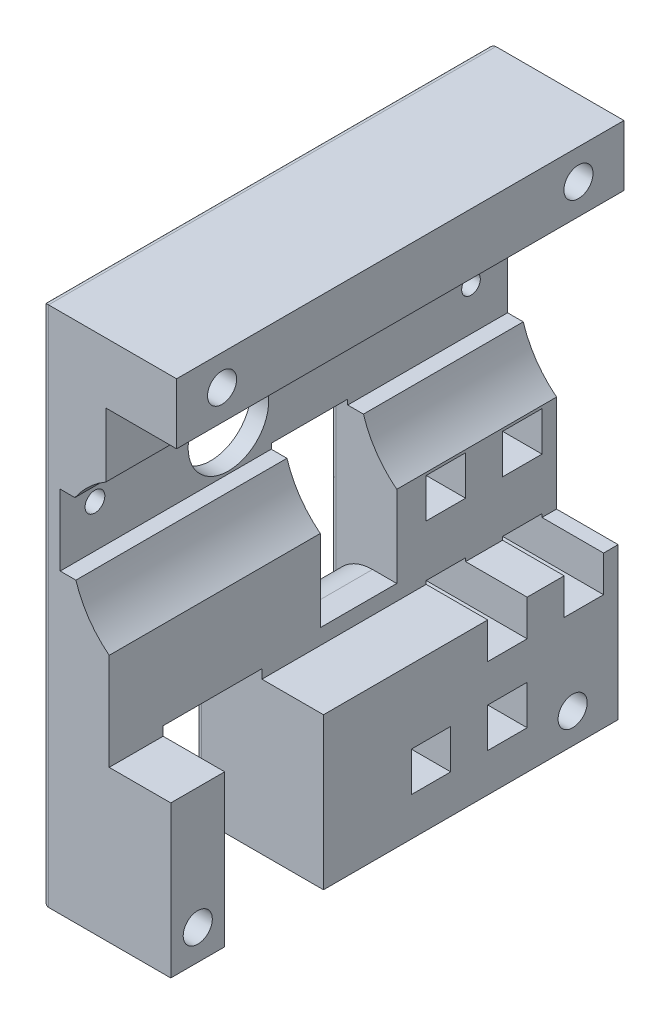
SolidWorks part; units mm, degrees
ref_plane "Front" through (0, 0, 0) normal (0, 0, 1) x (1, 0, 0)
ref_plane "Top" through (0, 0, 0) normal (0, 1, 0) x (1, 0, 0)
ref_plane "Right" through (0, 0, 0) normal (1, 0, 0) x (0, 0, -1)
sketch "Profile" plane through (0, 0, 0) normal (0, 0, 1) x (1, 0, 0)
  line L0 (9.3013, -54.1947) -> (9.3013, -29.1947)
  line L1 (-11.8487, -54.1947) -> (9.3013, -54.1947)
  line L2 (-11.8487, -54.1947) -> (-11.8487, 31.8453)
  line L3 (-11.8487, 31.8453) -> (10.2613, 31.8453)
  line L4 (10.2613, 21.8453) -> (10.2613, 31.8453)
  line L7 (9.3013, -29.1947) -> (-0.8487, -29.1947)
  line L8 (-0.8487, -29.1947) -> (-0.8487, -13.1966)
  line L10 (10.2613, 21.8453) -> (-1.3887, 21.8453)
  line L11 (-1.3887, 21.8453) -> (-1.3887, 11.2835)
  line L12 (-6.5097, 6.4953) -> (-8.9287, 6.4953)
  line L13 (-8.9287, 6.4953) -> (-8.9287, -5.2047)
  line L14 (-8.9287, -5.2047) -> (-6.3407, -5.2047)
  arc A0 (-6.3407, -5.2047) -> (-0.8487, -13.1966) centre (9.1973, -0.41) ccw
  arc A1 (-6.5097, 6.4953) -> (-1.3887, 11.2835) centre (6.8957, -2.7089) cw
  point P0 (0, 0)
  dimension "D15" = 16.261
  dimension "D16" = 16.261
  dimension "D1" = 86.04
  dimension "D2" = 22.11
  dimension "D3" = 10
  dimension "D4" = 25
  dimension "D5" = 21.15
  dimension "D6" = 10.15
  dimension "D7" = 11.65
  dimension "D8" = 10.5617
  dimension "D9" = 15.9981
  dimension "D10" = 2.588
  dimension "D11" = 11.7
  dimension "D12" = 2.4191
  dimension "D13" = 5.492
  dimension "D14" = 23.99
extrude "ProfileExtrude" add sketch "Profile" along normal blind 73.76
sketch "HoseWindow" plane through (-11.8487, 0, 0) normal (-1, 0, 0) x (0, 0, 1)
  line L0 (73.76, -54.1947) -> (0, -54.1947) construction
  line L1 (64.87, -54.1947) -> (48.58, -54.1947)
  line L2 (64.87, -54.1947) -> (64.87, -27.6947)
  line L3 (64.87, -27.6947) -> (48.58, -27.6947)
  line L4 (48.58, -54.1947) -> (48.58, -27.6947)
  dimension "D1" = 16.29
  dimension "D2" = 26.5
  dimension "D3" = 8.89
extrude "HoseWindowCut" cut sketch "HoseWindow" against normal through all
sketch "CageScrews" plane through (-11.8487, 0, 0) normal (-1, 0, 0) x (0, 0, 1)
  line L0 (73.76, 31.8453) -> (0, 31.8453) construction
  line L1 (0, 31.8453) -> (0, -54.1947) construction
  line L2 (73.76, 31.8453) -> (73.76, -54.1947) construction
  line L3 (73.76, -54.1947) -> (64.87, -54.1947) construction
  line L4 (48.58, -54.1947) -> (0, -54.1947) construction
  circle A0 centre (7.5, 26.8453) radius 2.4
  circle A1 centre (66.26, 26.8453) radius 2.4
  circle A2 centre (7.5, -49.1947) radius 2.4
  circle A3 centre (69.31, -49.1947) radius 2.4
  dimension "D1" = 4.8
  dimension "D2" = 5
  dimension "D3" = 7.5
  dimension "D4" = 7.5
  dimension "D5" = 5
  dimension "D6" = 5
  dimension "D7" = 4.45
  dimension "D8" = 5
  dimension "D9" = 7.5
extrude "CageScrewsCut" cut sketch "CageScrews" against normal through all
sketch "AxleHole" plane through (-11.8487, 0, 0) normal (-1, 0, 0) x (0, 0, 1)
  line L0 (46.03, -4.7837) -> (46.03, 6.7405) construction
  line L1 (47.361, 8.3595) -> (47.361, 6.7405)
  line L2 (47.361, 6.7405) -> (44.699, 6.7405)
  line L3 (44.699, 6.7405) -> (44.699, 8.3595)
  line L5 (48.58, -54.1947) -> (0, -54.1947) construction
  line L6 (0, 31.8453) -> (0, -54.1947) construction
  line L7 (39.391, 1.8553) -> (52.669, 1.8553) construction
  arc A0 (44.699, 8.3595) -> (47.361, 8.3595) centre (46.03, 1.8553) ccw
  dimension "D1" = 13.278
  dimension "D2" = 1.331
  dimension "D3" = 1.619
  dimension "D4" = 1.619
  dimension "D5" = 46.03
  dimension "D6" = 56.05
extrude "AxleHoleCut" cut sketch "AxleHole" against normal through all
sketch "SetScrewHoles" plane through (-11.8487, 0, 0) normal (-1, 0, 0) x (0, 0, 1)
  line L0 (47.361, 6.7405) -> (44.699, 6.7405) construction
  circle A0 centre (6.03, 1.8553) radius 1.5394
  circle A1 centre (68.03, 1.8553) radius 1.629
  point P6 (46.03, 6.7405)
  point P7 (46.03, 6.7405)
  dimension "D1" = 22
  dimension "D2" = 40
extrude "SetScrewHolesCut" cut sketch "SetScrewHoles" against normal through all
sketch "VelocityWindow" plane through (-11.8487, 0, 0) normal (-1, 0, 0) x (0, 0, 1)
  line L0 (73.76, 31.8453) -> (73.76, -54.1947) construction
  line L1 (38.96, -26.6447) -> (26.35, -26.6447)
  line L2 (38.96, -26.6447) -> (38.96, -4.3547)
  line L3 (38.96, -4.3547) -> (26.35, -4.3547)
  line L4 (26.35, -26.6447) -> (26.35, -4.3547)
  line L5 (38.96, -26.6447) -> (26.35, -4.3547) construction
  line L6 (38.96, -4.3547) -> (26.35, -26.6447) construction
  line L7 (48.58, -54.1947) -> (0, -54.1947) construction
  point P0 (32.655, -15.4997)
  dimension "D1" = 12.61
  dimension "D2" = 22.29
  dimension "D3" = 34.8
  dimension "D4" = 27.55
extrude "VelocityWindowCut" cut sketch "VelocityWindow" against normal through all
fillet "Fillet3" radius 7 1 edges at (-11.8487, -26.6447, 32.655)
sketch "TriggerRackSlotCut" plane through (-11.8487, 0, 0) normal (-1, 0, 0) x (0, 0, 1)
  line L0 (15, -41.3447) -> (21.5, -41.3447)
  line L1 (15, -41.3447) -> (15, -47.8447)
  line L2 (21.5, -41.3447) -> (21.5, -47.8447)
  line L3 (15, -47.8447) -> (21.5, -47.8447)
  line L4 (0, 31.8453) -> (0, -54.1947) construction
  line L5 (27.6, -41.3447) -> (34.1, -41.3447)
  line L6 (27.6, -41.3447) -> (27.6, -47.8447)
  line L7 (34.1, -41.3447) -> (34.1, -47.8447)
  line L8 (27.6, -47.8447) -> (34.1, -47.8447)
  line L9 (2.4, -28.6447) -> (8.9, -28.6447)
  line L10 (2.4, -28.6447) -> (2.4, -35.1447)
  line L11 (8.9, -28.6447) -> (8.9, -35.1447)
  line L12 (2.4, -35.1447) -> (8.9, -35.1447)
  line L13 (15, -28.6447) -> (21.5, -28.6447)
  line L14 (15, -28.6447) -> (15, -35.1447)
  line L15 (21.5, -28.6447) -> (21.5, -35.1447)
  line L16 (48.58, -54.1947) -> (0, -54.1947) construction
  line L17 (15, -35.1447) -> (21.5, -35.1447)
  line L18 (15, -41.3447) -> (27.6, -41.3447) construction
  line L19 (15, -41.3447) -> (15, -28.6447) construction
  line L20 (2.4, -13.6447) -> (8.9, -13.6447)
  line L21 (2.4, -13.6447) -> (2.4, -20.1447)
  line L22 (8.9, -13.6447) -> (8.9, -20.1447)
  line L23 (2.4, -20.1447) -> (8.9, -20.1447)
  line L24 (15, -13.6447) -> (21.5, -13.6447)
  line L25 (15, -13.6447) -> (15, -20.1447)
  line L26 (21.5, -13.6447) -> (21.5, -20.1447)
  line L27 (15, -20.1447) -> (21.5, -20.1447)
  line L28 (15, -28.6447) -> (2.4, -28.6447) construction
  line L43 (27.6, -28.6447) -> (34.1, -28.6447) [skipped]
  line L44 (27.6, -28.6447) -> (27.6, -35.1447) [skipped]
  line L45 (34.1, -28.6447) -> (34.1, -35.1447) [skipped]
  line L46 (27.6, -35.1447) -> (34.1, -35.1447) [skipped]
  dimension "D1" = 6.35
  dimension "D2" = 15
  dimension "D3" = 6.5
  dimension "D4" = 6.5
  dimension "D7" = 2
  dimension "D5" = 12.6
  dimension "D6" = 12.7
  dimension "D9" = 12.6
  dimension "D8" = 2
extrude "RackSlotCut" cut sketch "TriggerRackSlotCut" against normal through all
fillet "Fillet4" radius 1 35 edges at (-11.8487, -31.8947, 21.5) (-11.8487, -28.6447, 18.25) (-11.8487, -31.8947, 15) (-11.8487, -35.1447, 18.25) (-11.8487, -47.8447, 18.25) (-11.8487, -44.5947, 15) (-11.8487, -41.3447, 18.25) (-11.8487, -44.5947, 21.5) (-11.8487, -47.8447, 30.85) (-11.8487, -44.5947, 34.1) (-11.8487, -18.9997, 38.96) (-11.8487, -4.3547, 32.655) (-11.8487, -18.9997, 26.35) (-11.8487, -11.1747, 0) (-11.8487, -54.1947, 24.29) (-11.8487, -40.9447, 48.58) (-11.8487, -27.6947, 56.725) (-11.8487, -40.9447, 64.87) (-11.8487, -54.1947, 69.315) (-11.8487, -11.1747, 73.76) (-11.8487, 31.8453, 36.88) (-11.8487, -44.5947, 27.6) (-11.8487, -41.3447, 30.85) (-11.8487, -35.1447, 5.65) (-11.8487, -31.8947, 2.4) (-11.8487, -31.8947, 8.9) (-11.8487, -28.6447, 5.65) (-11.8487, -13.6447, 18.25) (-11.8487, -16.8947, 21.5) (-11.8487, -20.1447, 18.25) (-11.8487, -16.8947, 15) (-11.8487, -16.8947, 2.4) (-11.8487, -20.1447, 5.65) (-11.8487, -16.8947, 8.9) (-11.8487, -13.6447, 5.65)
equation "\"BottomEdge\"=21.15mm"
equation "\"TopEdge\"=22.11mm"
equation "\"TotalHeight\"=86.04mm"
equation "\"TotalLength\"=73.76mm"
equation "\"ScrewClearance\"=10mm"
equation "\"TopDepth\"= 11.65mm"
equation "\"BottomDepth\"=10.15mm"
equation "\"TopHeight\"=10.56175mm"
equation "\"BottomHeight\"=15.99813mm"
equation "\"TopChannelDepth\"=2.41908mm"
equation "\"BottomChannelDepth\"=2.588mm"
equation "\"ChannelHeight\"=11.7mm"
equation "\"ChanRelHeight\"=23.99mm"
equation "\"ChanRelDepth\"=5.492mm"
equation "\"ChamberRadius\"=16.261mm"
equation "\"CageScrewDiameter\"=4.8mm"
equation "\"SetScrewDiameter\"=3.5mm"
equation "\"AxleRadius\"=6.639mm"
equation "\"KeyHeight\"=1.619mm"
equation "\"KeyWidth\"=2.662mm"
equation "\"HoseWindowWidth\"=16.29mm"
equation "\"HoseWindowHeight\"=26.5mm"
equation "\"HoseWindow-Edge\"=8.89mm"
equation "\"CageScrew-VerticalEdge\"=5.0mm"
equation "\"CageScrew-HorizontalEdge\"=7.5mm"
equation "\"CageScrew-HoseCornerScrewEdge\"=4.45mm"
equation "\"Axle-BottomEdge\"=56.05mm"
equation "\"BackSetScrew-Axel\"=40mm"
equation "\"FrontSetScrew-Axel\"=22mm"
equation "\"VelocityWindow-Backedge\"=34.8mm"
equation "\"velocityWindow-bottomedge\"=27.55mm"
equation "\"VelocityWindowHeight\"=22.29mm"
equation "\"VelocityWindowWidth\"=12.61mm"
equation "\"D11@Profile\"= \"ChannelHeight\""
equation "\"D10@Profile\"= \"BottomChannelDepth\""
equation "\"D12@Profile\"= \"TopChannelDepth\""
equation "\"D8@Profile\" = \"TopHeight\""
equation "\"D9@Profile\"= \"BottomHeight\""
equation "\"D6@Profile\"= \"BottomDepth\""
equation "\"D7@Profile\"= \"TopDepth\""
equation "\"D3@Profile\"= \"ScrewClearance\""
equation "\"ScrewClearanceBottom\"=25mm"
equation "\"D4@Profile\"=\"ScrewClearanceBottom\""
equation "\"D5@Profile\"=\"BottomEdge\""
equation "\"D2@Profile\"= \"TopEdge\""
equation "\"D1@Profile\"= \"TotalHeight\""
equation "\"D13@Profile\"= \"ChanRelDepth\""
equation "\"D14@Profile\"= \"ChanRelHeight\""
equation "\"D15@Profile\"= \"ChamberRadius\""
equation "\"D16@Profile\"= \"ChamberRadius\""
equation "\"D1@ProfileExtrude\"= \"TotalLength\""
equation "\"D3@HoseWindow\"= \"HoseWindow-Edge\""
equation "\"D2@HoseWindow\"= \"HoseWindowHeight\""
equation "\"D1@HoseWindow\"= \"HoseWindowWidth\""
equation "\"D1@CageScrews\"= \"CageScrewDiameter\""
equation "\"D9@CageScrews\" = \"CageScrew-HorizontalEdge\""
equation "\"D7@CageScrews\" = \"CageScrew-HoseCornerScrewEdge\""
equation "\"D4@CageScrews\" = \"CageScrew-HorizontalEdge\""
equation "\"D6@CageScrews\"= \"CageScrew-VerticalEdge\""
equation "\"D5@CageScrews\"= \"CageScrew-VerticalEdge\""
equation "\"D8@CageScrews\"= \"CageScrew-VerticalEdge\""
equation "\"D2@CageScrews\"= \"CageScrew-VerticalEdge\""
equation "\"D1@AxleHole\"= \"AxleRadius\" * 2"
equation "\"D4@AxleHole\"= \"KeyHeight\""
equation "\"D3@AxleHole\"= \"KeyHeight\""
equation "\"D2@AxleHole\"= \"KeyWidth\" / 2"
equation "\"Axle-FrontEdge\"=46.03mm"
equation "\"D6@AxleHole\"= \"Axle-BottomEdge\""
equation "\"D5@AxleHole\"= \"Axle-FrontEdge\""
equation "\"D2@SetScrewHoles\"= \"BackSetScrew-Axel\""
equation "\"D1@SetScrewHoles\"= \"FrontSetScrew-Axel\""
equation "\"D1@VelocityWindow\"= \"VelocityWindowWidth\""
equation "\"D2@VelocityWindow\"= \"VelocityWindowHeight\""
equation "\"D3@VelocityWindow\"= \"VelocityWindow-Backedge\""
equation "\"D4@VelocityWindow\"= \"velocityWindow-bottomedge\""
equation "\"bottomslotheight\"=6.35mm"
equation "\"D1@TriggerRackSlotCut\"=\"bottomslotheight\""
equation "\"FrontSlotDepth\"=15mm"
equation "\"SlotSize\"=6.5mm"
equation "\"D3@TriggerRackSlotCut\"=\"SlotSize\""
equation "\"D4@TriggerRackSlotCut\"=\"SlotSize\""
equation "\"D2@TriggerRackSlotCut\"=\"FrontSlotDepth\""
